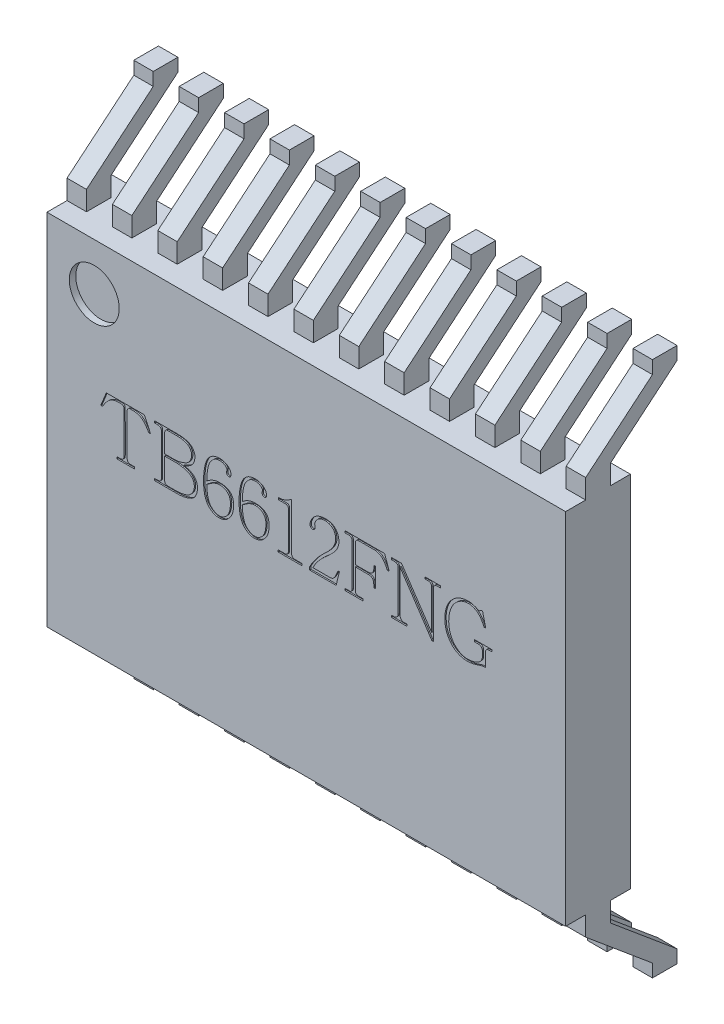
SolidWorks part; units mm, degrees
ref_plane "Plan de face" through (0, 0, 0) normal (0, 0, 1) x (1, 0, 0)
ref_plane "Plan de dessus" through (0, 0, 0) normal (0, 1, 0) x (1, 0, 0)
ref_plane "Plan de droite" through (0, 0, 0) normal (1, 0, 0) x (0, 0, -1)
sketch "Esquisse1" plane through (0, 0, 0) normal (0, 0, 1) x (1, 0, 0)
  line L0 (-6.4232, 0) -> (8.5456, 0) construction
  line L1 (0, -6.4764) -> (0, 6.8796) construction
  line L3 (-4, 2.77) -> (4, 2.77)
  line L4 (-4, 2.77) -> (-4, -2.77)
  line L5 (-4, -2.77) -> (4, -2.77)
  line L6 (4, 2.77) -> (4, -2.77)
  dimension "D1" = 8
  dimension "D2" = 5.54
extrude "Corps" add sketch "Esquisse1" along normal blind 1
sketch "Esquisse2" plane through (0, 0, 1) normal (0, 0, 1) x (1, 0, 0)
  line L0 (4, 2.77) -> (-4, 2.77) construction
  line L2 (-4, 2.77) -> (-4, -2.77) construction
  circle A0 centre (-3.27, 2.04) radius 0.385
  dimension "D3" = 0.77
  dimension "D1" = 0.73
  dimension "D2" = 0.73
extrude "Enlèv. mat.-Extru.1" cut sketch "Esquisse2" against normal blind 0.1
sketch "Esquisse3" plane through (0, 0, 1) normal (0, 0, 1) x (1, 0, 0)
  text T0 "TB6612FNG" font "@Adobe Ming Std L" height 0.8
extrude "Texte" cut sketch "Esquisse3" against normal blind 0.02
ref_plane "Plan1" through (0, -2.27, 0) normal (0, -1, 0) x (-1, 0, 0)
ref_plane "Plan2" through (-4, 0, 0) normal (-1, 0, 0) x (0, 0, 1)
sketch "Esquisse6" plane through (-4, 0, 0) normal (-1, 0, 0) x (0, 0, 1)
  line L10 (0.31, -3.07) -> (0.31, -2.77)
  line L11 (1, -2.77) -> (0, -2.77) construction
  line L12 (0.69, -3.07) -> (0.69, -2.77)
  line L13 (0.31, -2.77) -> (0.69, -2.77)
  line L14 (0, 2.77) -> (0, -2.77) construction
  line L15 (0.31, -3.07) -> (-0.7199, -3.93)
  line L16 (-0.7199, -3.93) -> (-0.7199, -4.13)
  line L17 (-0.7199, -4.13) -> (-0.34, -4.13)
  line L18 (-0.34, -4.13) -> (-0.34, -3.93)
  line L19 (-0.34, -3.93) -> (0.69, -3.07)
  point P22 (-0.34, -4.03)
  dimension "D10" = 0.3
  dimension "D11" = 0.31
  dimension "D12" = 0.38
  dimension "D13" = 0.3799
  dimension "D14" = 1.03
  dimension "D15" = 0.2
  dimension "D16" = 0.2
  dimension "D17" = 0.86
extrude "Boss.-Extru.3" add sketch "Esquisse6" against normal blind 0.3
pattern_linear "Répétition linéaire2" count 12 spacing 0.7 along (1, 0, 0) of "Boss.-Extru.3"
mirror "Symétrie1" about plane through (0, 0, 0) normal (0, 1, 0) of "Répétition linéaire2", "Boss.-Extru.3"
